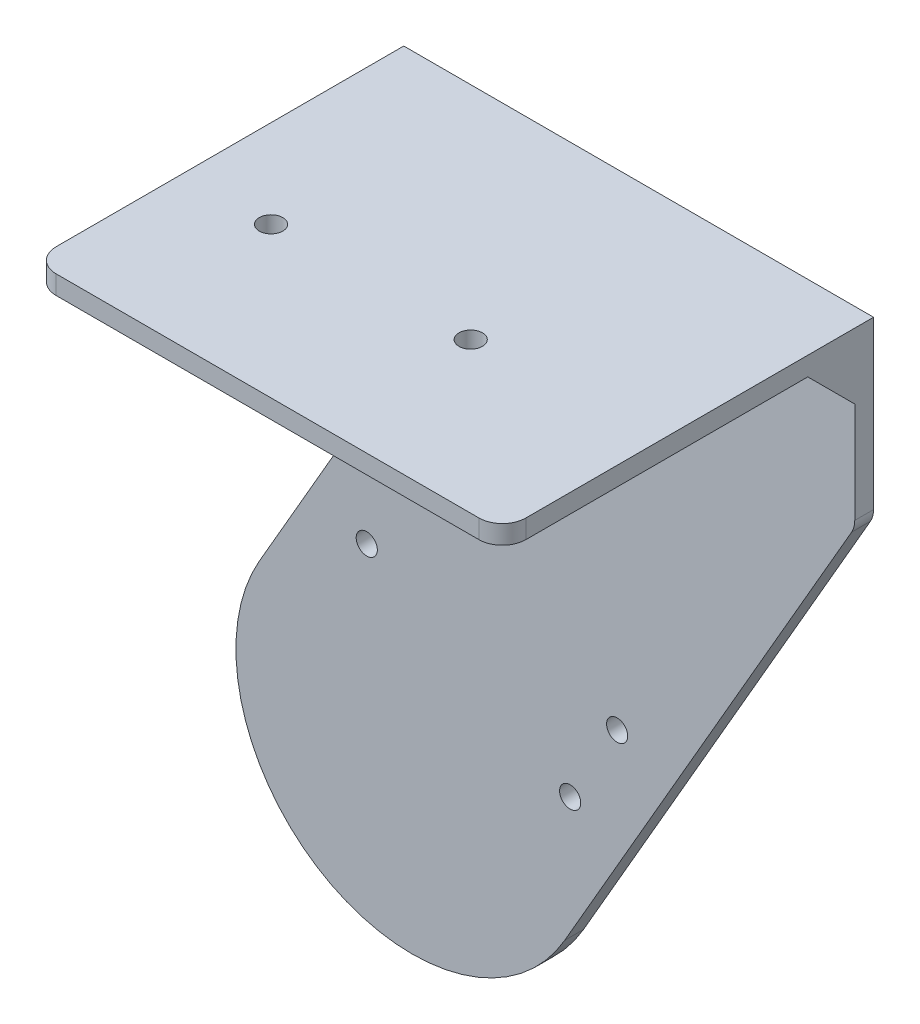
SolidWorks part; units mm, degrees
ref_plane "Front Plane" through (0, 0, 0) normal (0, 0, 1) x (1, 0, 0)
ref_plane "Top Plane" through (0, 0, 0) normal (0, 1, 0) x (1, 0, 0)
ref_plane "Right Plane" through (0, 0, 0) normal (1, 0, 0) x (0, 0, -1)
sketch "Sketch1" plane through (0, 0, 0) normal (0, 0, 1) x (1, 0, 0)
  line L0 (0, 0) -> (40.2373, 0) construction
  line L1 (64.9519, -37.5) -> (0, 0) construction
  line L2 (0, 0) -> (-64.9519, 37.5) construction
  line L3 (-64.9519, 37.5) -> (-11.547, 130)
  line L4 (64.9519, -37.5) -> (188.453, 176.4102)
  line L5 (-11.547, 130) -> (-11.547, 250)
  line L6 (-11.547, 250) -> (188.453, 250)
  line L7 (188.453, 250) -> (188.453, 176.4102)
  arc A0 (64.9519, -37.5) -> (-64.9519, 37.5) centre (0, 0) cw
  dimension "D2" = 75
  dimension "D1" = 30
  dimension "D4" = 130
  dimension "D5" = 200
  dimension "D6" = 120
extrude "Boss-Extrude1" add sketch "Sketch1" along normal blind 8
sketch "Sketch4" plane through (-11.547, 0, 0) normal (-1, 0, 0) x (0, 0, 1)
  line L0 (8, 250) -> (158, 250)
  line L1 (158, 250) -> (158, 242)
  line L2 (158, 242) -> (8, 242)
  line L3 (8, 250) -> (8, 130) construction
  line L4 (8, 242) -> (8, 250)
  line L8 (0, 250) -> (0, 130)
  line L9 (0, 130) -> (8, 130)
  line L10 (8, 130) -> (8, 250)
  line L11 (8, 250) -> (0, 250)
  line L13 (0, 130) -> (8, 130)
  line M10 (8, 130) -> (8, 250)
  dimension "D1" = 8
  dimension "D2" = 150
  dimension "D3" = 0
extrude "Boss-Extrude2" add sketch "Sketch4" along direction (-1, 0, 0) on the side against the normal up to surface (200 mm away) contours L2 L1 L0 M10
chamfer "Chamfer1" distance 20 angle 45 1 edges at (88.453, 242, 8)
sketch "Sketch5" plane through (0, 250, 0) normal (0, 1, 0) x (1, 0, 0)
  line L0 (188.453, -158) -> (188.453, 0) construction
  line L2 (68.453, -94) -> (68.453, -158) construction
  line L3 (188.453, -158) -> (-11.547, -158) construction
  line L4 (25.953, -94) -> (68.453, -94) construction
  line L5 (68.453, -94) -> (110.953, -94) construction
  circle A0 centre (68.453, -94) radius 10 construction
  circle A1 centre (25.953, -94) radius 5
  circle A2 centre (110.953, -94) radius 5
  dimension "D3" = 20
  dimension "D5" = 10
  dimension "D1" = 120
  dimension "D2" = 64
  dimension "D4" = 85
extrude "Cut-Extrude1" cut sketch "Sketch5" against normal up to next
sketch "Sketch6" plane through (0, 0, 8) normal (0, 0, 1) x (1, 0, 0)
  line L0 (-32.9519, 92.9256) -> (96.9519, 17.9256) construction
  line L1 (-11.547, 130) -> (-64.9519, 37.5) construction
  line L2 (64.9519, -37.5) -> (188.453, 176.4102) construction
  line L3 (-32.9519, 92.9256) -> (-28.9519, 99.8538) construction
  line L4 (-28.9519, 99.8538) -> (100.9519, 24.8538) construction
  line L5 (100.9519, 24.8538) -> (96.9519, 17.9256) construction
  line L6 (0.6987, 101.2102) -> (-19.3013, 66.5692) construction
  line L7 (-19.3013, 66.5692) -> (67.3013, 16.5692) construction
  line L8 (67.3013, 16.5692) -> (87.3013, 51.2102) construction
  line L9 (87.3013, 51.2102) -> (0.6987, 101.2102) construction
  line L10 (0.6987, 101.2102) -> (-20.9519, 113.7102) construction
  line L11 (87.3013, 51.2102) -> (108.9519, 38.7102) construction
  circle A0 centre (0.6987, 101.2102) radius 4.5
  circle A1 centre (87.3013, 51.2102) radius 4.5
  circle A2 centre (67.3013, 16.5692) radius 4.5
  circle A3 centre (-19.3013, 66.5692) radius 4.5
  dimension "D6" = 9
  dimension "D1" = 64
  dimension "D2" = 8
  dimension "D3" = 100
  dimension "D4" = 16
  dimension "D5" = 16
extrude "Cut-Extrude2" cut sketch "Sketch6" against normal up to next
fillet "Fillet1" radius 10 4 edges at (-11.547, 130, 4) (188.453, 176.4102, 4) (188.453, 246, 158) (-11.547, 246, 158)
